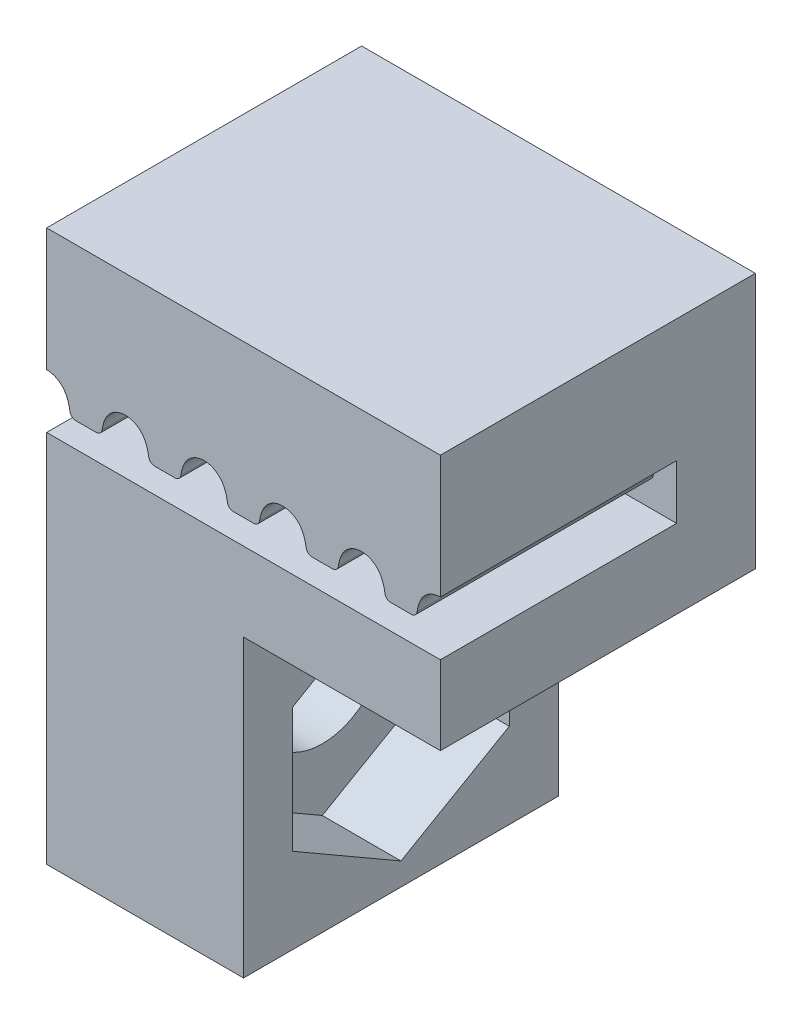
SolidWorks part; units mm, degrees
material "ABS"
ref_plane "Front Plane" through (0, 0, 0) normal (0, 0, 1) x (1, 0, 0)
ref_plane "Top Plane" through (0, 0, 0) normal (0, 1, 0) x (1, 0, 0)
ref_plane "Right Plane" through (0, 0, 0) normal (1, 0, 0) x (0, 0, -1)
sketch "Sketch3" plane through (0, 0, 0) normal (0, 0, 1) x (1, 0, 0)
  line L1 (0, -2) -> (10, -2)
  line L2 (0, -2) -> (0, 4.5)
  line L3 (0, 4.5) -> (10, 4.5)
  line L4 (10, -2) -> (10, 4.5)
  dimension "D1" = 10
  dimension "D2" = 6.5
  dimension "D3" = 2
extrude "Boss-Extrude2" add sketch "Sketch3" along normal blind 8
sketch "Sketch1" plane through (0, 0, 0) normal (0, 0, 1) x (1, 0, 0)
  line L4 (1, 0.63) -> (1, 1.38) construction
  line L5 (0.7402, 0.63) -> (1.2598, 0.63)
  line L6 (2, 1.38) -> (2, 0)
  line L9 (0, 1.38) -> (0, 0)
  line L10 (0, 0) -> (2, 0)
  arc A0 (1.2598, 0.63) -> (1.4085, 0.7604) centre (1.2598, 0.78) ccw
  arc A1 (1.4085, 0.7604) -> (1.5011, 1.0682) centre (2.4, 0.63) cw
  arc A2 (1.5011, 1.0682) -> (2, 1.38) centre (2, 0.825) cw
  arc A3 (0.4989, 1.0682) -> (0, 1.38) centre (0, 0.825) ccw
  arc A4 (0.5915, 0.7604) -> (0.4989, 1.0682) centre (-0.4, 0.63) ccw
  arc A5 (0.7402, 0.63) -> (0.5915, 0.7604) centre (0.7402, 0.78) cw
  dimension "D1" = 0.555
  dimension "D2" = 1
  dimension "D3" = 0.15
  dimension "D4" = 0.4
  dimension "D5" = 0.75
  dimension "D6" = 2
  dimension "D7" = 1.38
extrude "Cut-Extrude1" cut sketch "Sketch1" along normal blind 6 from offset 2
pattern_linear "LPattern2" count 7 spacing 2 along (1, 0, 0) of "Cut-Extrude1"
sketch "Sketch4" plane through (0, 0, 0) normal (-1, 0, 0) x (0, 0, 1)
  line L0 (0, 4.5) -> (0, -2) construction
  line L1 (0, -2) -> (8, -2)
  line L2 (0, -2) -> (0, -9.5)
  line L3 (0, -9.5) -> (8, -9.5)
  line L4 (8, -2) -> (8, -9.5)
  dimension "D1" = 7.5
  dimension "D2" = 8
extrude "Boss-Extrude3" add sketch "Sketch4" against normal blind 5
sketch "Sketch5" plane through (0, 0, 0) normal (-1, 0, 0) x (0, 0, 1)
  line L0 (4, -9.5) -> (4, -5.75) construction
  line L1 (0, -9.5) -> (8, -9.5) construction
  line L2 (4, -5.75) -> (0, -5.75) construction
  line L4 (4, -5.75) -> (8, -5.75) construction
  line L5 (1.25, -4.1623) -> (1.25, -7.3377)
  line L6 (1.25, -7.3377) -> (4, -8.9254)
  line L7 (4, -8.9254) -> (6.75, -7.3377)
  line L8 (6.75, -7.3377) -> (6.75, -4.1623)
  line L9 (6.75, -4.1623) -> (4, -2.5746)
  line L10 (4, -2.5746) -> (1.25, -4.1623)
  line L11 (8, -9.5) -> (8, -2) construction
  line L12 (4, -5.75) -> (4, -2) construction
  circle A0 centre (4, -5.75) radius 2.75 construction
  dimension "D1" = 3.75
  dimension "D2" = 5.5
extrude "Cut-Extrude2" cut sketch "Sketch5" against normal blind 2 from offset 3 offset against normal yes
sketch "Sketch6" plane through (3, 0, 0) normal (-1, 0, 0) x (0, 0, 1)
  line L0 (4, -2.5746) -> (4, -8.9254) construction
  circle A0 centre (4, -5.75) radius 1.6
  dimension "D1" = 3.2
extrude "Cut-Extrude3" cut sketch "Sketch6" along normal blind 10
